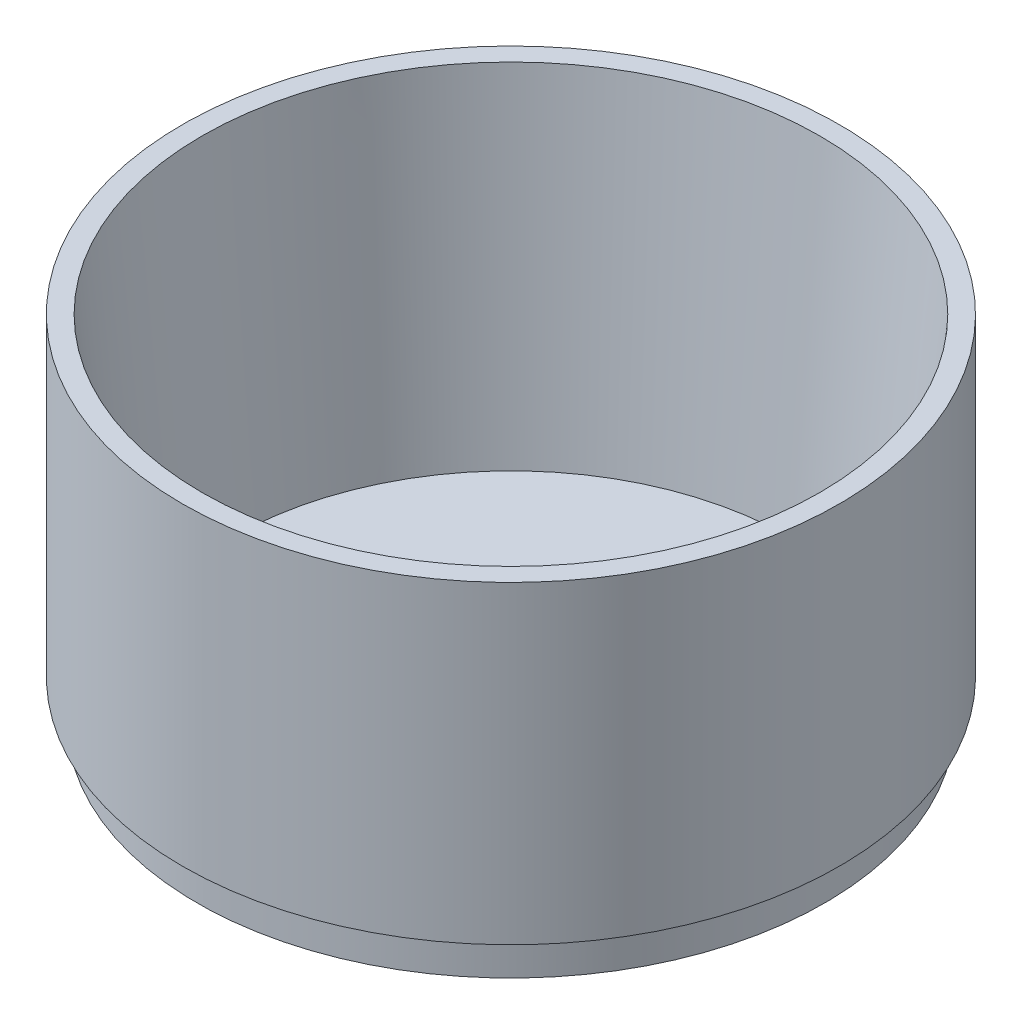
SolidWorks part; units mm, degrees
material "PLA"
ref_plane "Front Plane" through (0, 0, 0) normal (0, 0, 1) x (1, 0, 0)
ref_plane "Top Plane" through (0, 0, 0) normal (0, 1, 0) x (1, 0, 0)
ref_plane "Right Plane" through (0, 0, 0) normal (1, 0, 0) x (0, 0, -1)
sketch "Sketch1" plane through (0, 0, 0) normal (0, 1, 0) x (1, 0, 0)
  circle A0 centre (0, 0) radius 53.1812
  dimension "D1" = 106.3625
extrude "Boss-Extrude1" add sketch "Sketch1" along normal blind 50.8
sketch "Sketch2" plane through (0, 0, 0) normal (0, -1, 0) x (1, 0, 0)
  circle A0 centre (0, 0) radius 50.8
  circle A1 centre (0, 0) radius 47.625
  dimension "D1" = 101.6
  dimension "D2" = 95.25
extrude "Boss-Extrude2" add sketch "Sketch2" along normal blind 6.35 contours A1 | A0 A1
sketch "Sketch3" plane through (0, 50.8, 0) normal (0, 1, 0) x (1, 0, 0)
  circle A0 centre (0, 0) radius 50.0062
  dimension "D1" = 100.0125
extrude "Cut-Extrude1" cut sketch "Sketch3" against normal offset from surface 3.175 draft 5 contours A0
sketch "Sketch4" plane through (0, -3.175, 0) normal (0, 1, 0) x (1, 0, 0)
  circle A0 centre (7.4871, -15.776) radius 4.7625 construction
  circle A1 centre (0, 0) radius 45.284
  circle A3 centre (-7.4871, 15.776) radius 4.7625 construction
  circle A4 centre (0, 0) radius 4.7625 construction
  circle A5 centre (7.4871, -15.776) radius 4.7625
  circle A6 centre (-7.4871, 15.776) radius 4.7625
  circle A7 centre (0, 0) radius 4.7625
  circle A10 centre (0, 0) radius 45.284
  dimension "D1" = 0
extrude "Cut-Extrude3" cut sketch "Sketch4" against normal up to surface (3.175 mm away) contours A5 | A7 | A6 up to face at (0, -6.35, -50.8)
